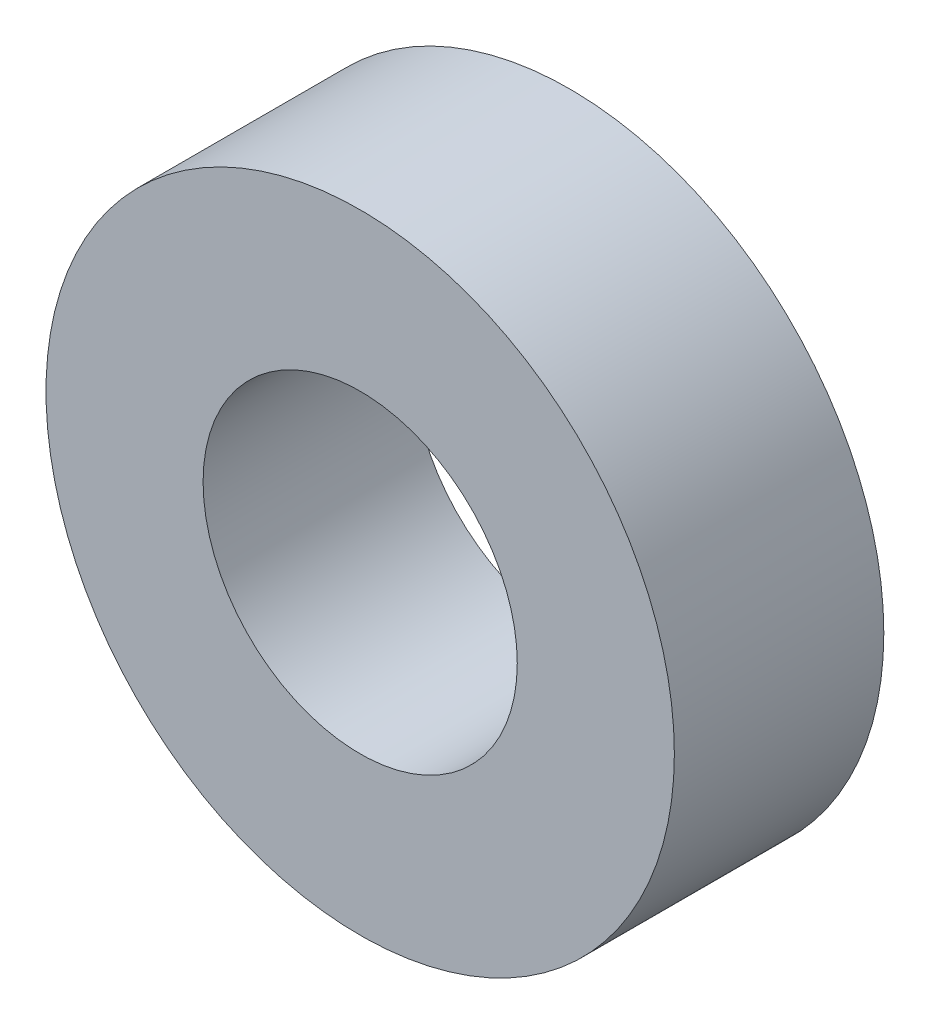
SolidWorks part; units mm, degrees
material "普通碳钢"
ref_plane "前视基准面" through (0, 0, 0) normal (0, 0, 1) x (1, 0, 0)
ref_plane "上视基准面" through (0, 0, 0) normal (0, 1, 0) x (1, 0, 0)
ref_plane "右视基准面" through (0, 0, 0) normal (1, 0, 0) x (0, 0, -1)
sketch "草图1" plane through (0, 0, 0) normal (0, 0, 1) x (1, 0, 0)
  circle A0 centre (0, 0) radius 6
  circle A1 centre (0, 0) radius 3
  dimension "D1" = 6
  dimension "D2" = 12
extrude "凸台-拉伸1" add sketch "草图1" along normal blind 4
